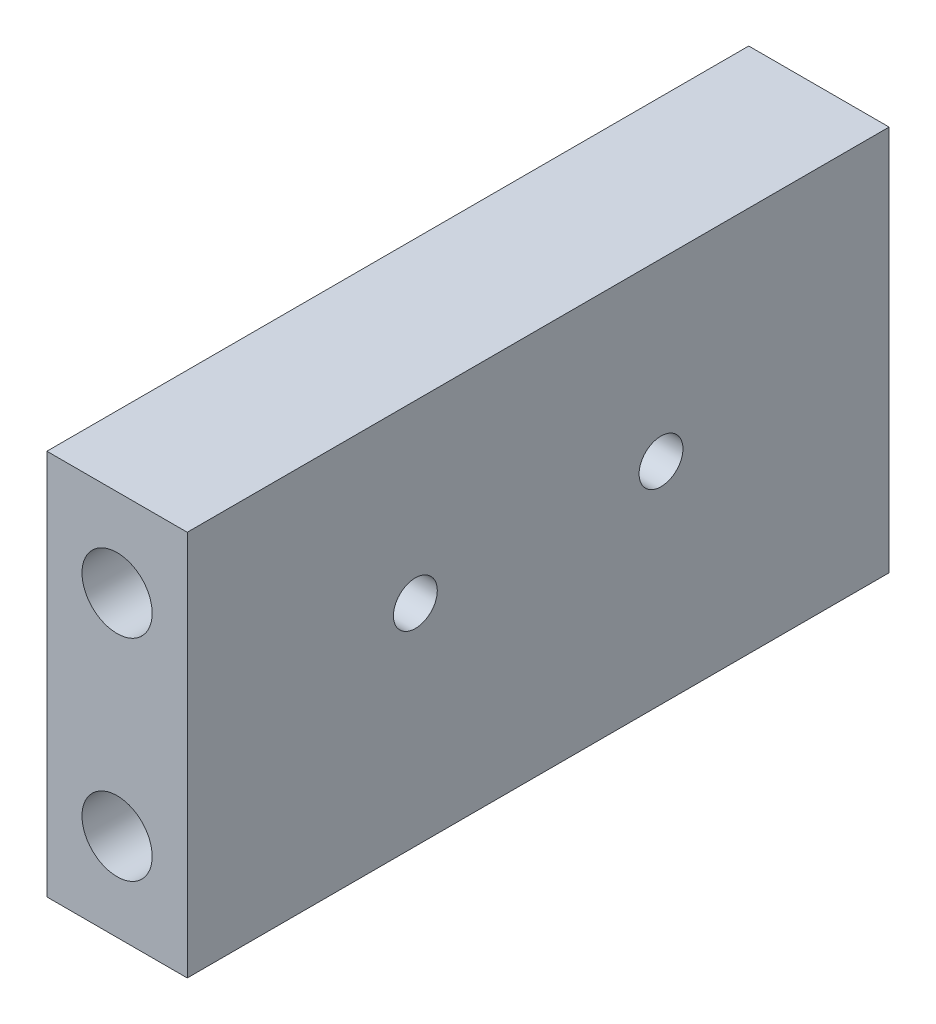
SolidWorks part; units mm, degrees
material "6061-T6 (SS)"
ref_plane "Front Plane" through (0, 0, 0) normal (0, 0, 1) x (1, 0, 0)
ref_plane "Top Plane" through (0, 0, 0) normal (0, 1, 0) x (1, 0, 0)
ref_plane "Right Plane" through (0, 0, 0) normal (1, 0, 0) x (0, 0, -1)
sketch "Sketch1" plane through (0, 0, 0) normal (1, 0, 0) x (0, 0, -1)
  line L1 (63.5, -34.925) -> (-63.5, -34.925)
  line L2 (63.5, -34.925) -> (63.5, 34.925)
  line L3 (63.5, 34.925) -> (-63.5, 34.925)
  line L4 (-63.5, -34.925) -> (-63.5, 34.925)
  line L5 (63.5, -34.925) -> (-63.5, 34.925) construction
  line L6 (63.5, 34.925) -> (-63.5, -34.925) construction
  point P0 (0, 0)
  dimension "D1" = 127
  dimension "D2" = 69.85
extrude "Boss-Extrude1" add sketch "Sketch1" along normal blind 25.4
sketch "Sketch2" plane through (0, 0, 63.5) normal (0, 0, 1) x (1, 0, 0)
  line L0 (12.7, 34.925) -> (12.7, -34.925)
  line L1 (25.4, 34.925) -> (0, 34.925) construction
  line L2 (25.4, -34.925) -> (0, -34.925) construction
  circle A0 centre (12.7, 19.05) radius 6.35
  circle A1 centre (12.7, -19.05) radius 6.35
  dimension "D1" = 12.7
  dimension "D2" = 12.7
  dimension "D3" = 15.875
  dimension "D4" = 15.875
extrude "Cut-Extrude1" cut sketch "Sketch2" against normal blind 25.4 contours A0 | A1
mirror "Mirror1" about plane through (0, 0, 0) normal (0, 0, 1) of "Cut-Extrude1"
sketch "Sketch3" plane through (25.4, 0, 0) normal (1, 0, 0) x (0, 0, -1)
  line L0 (63.5, 34.925) -> (-63.5, 34.925) construction
  circle A0 centre (-22.225, 3.175) radius 3.9688
  circle A1 centre (22.225, 3.175) radius 3.9688
  dimension "D1" = 44.45
  dimension "D2" = 7.9375
  dimension "D3" = 22.225
  dimension "D4" = 31.75
  dimension "D5" = 31.75
extrude "Cut-Extrude2" cut sketch "Sketch3" against normal through all
